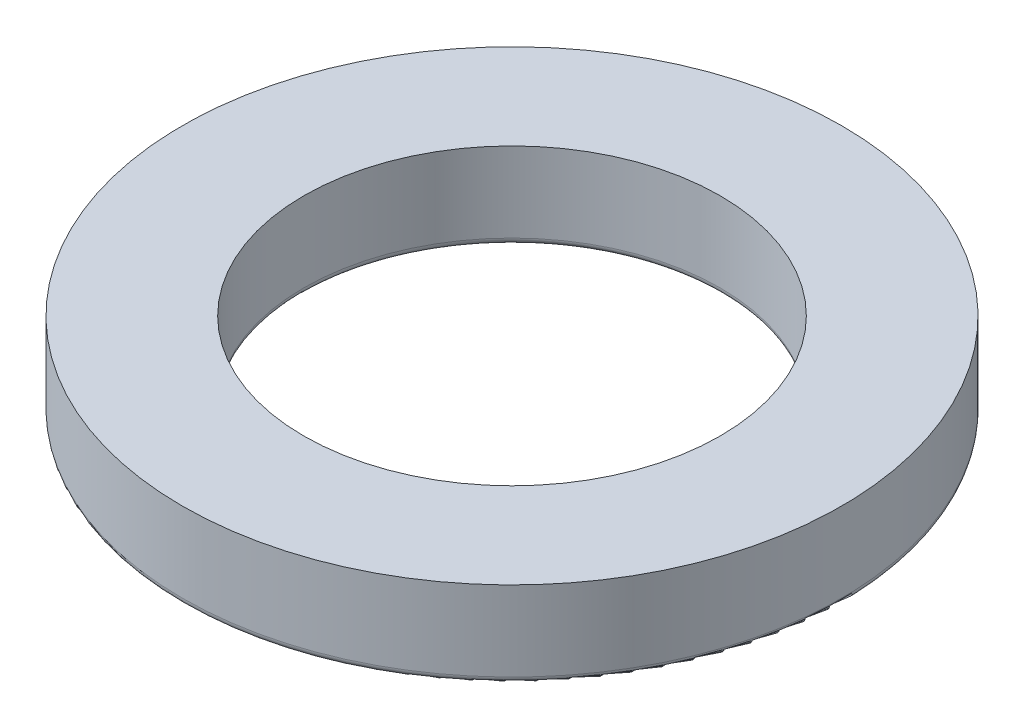
SolidWorks part; units mm, degrees
ref_plane "Front Plane" through (0, 0, 0) normal (0, 0, 1) x (1, 0, 0)
ref_plane "Top Plane" through (0, 0, 0) normal (0, 1, 0) x (1, 0, 0)
ref_plane "Right Plane" through (0, 0, 0) normal (1, 0, 0) x (0, 0, -1)
sketch "Sketch1" plane through (0, 0, 0) normal (0, 1, 0) x (1, 0, 0)
  circle A0 centre (0, 0) radius 9.5
  circle A1 centre (0, 0) radius 6
  dimension "D1" = 19
  dimension "D2" = 12
extrude "Boss-Extrude1" add sketch "Sketch1" along normal blind 2.5
fillet "Fillet1" radius 0.2 2 edges at (0, 0, 6) (0, 0, 9.5)
